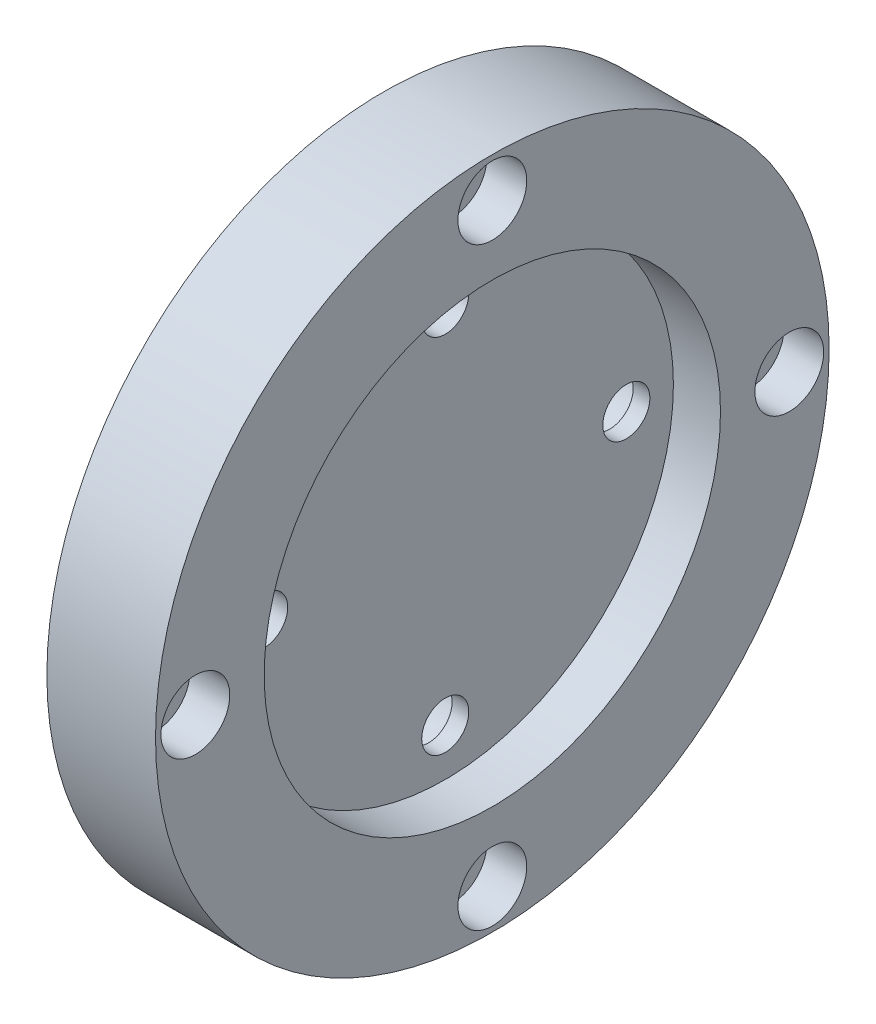
SolidWorks part; units mm, degrees
ref_plane "前视基准面" through (0, 0, 0) normal (0, 0, 1) x (1, 0, 0)
ref_plane "上视基准面" through (0, 0, 0) normal (0, 1, 0) x (1, 0, 0)
ref_plane "右视基准面" through (0, 0, 0) normal (1, 0, 0) x (0, 0, -1)
sketch "草图1" plane through (0, 0, 0) normal (1, 0, 0) x (0, 0, -1)
  circle A0 centre (0, 0) radius 46.5
  dimension "D1" = 93
extrude "凸台-拉伸1" add sketch "草图1" along normal blind 15
sketch "草图2" plane through (15, 0, 0) normal (1, 0, 0) x (0, 0, -1)
  circle A0 centre (0, 0) radius 31.5
  dimension "D1" = 63
extrude "切除-拉伸1" cut sketch "草图2" against normal blind 6.5
sketch "草图3" plane through (8.5, 0, 0) normal (1, 0, 0) x (0, 0, -1)
  circle A0 centre (0, 0) radius 25 construction
  circle A1 centre (0, 25) radius 3.25
  dimension "D1" = 50
  dimension "D2" = 6.5
extrude "切除-拉伸2" cut sketch "草图3" against normal through all
pattern_circular "阵列(圆周)1" count 4 over 360 about axis through (0, 0, 0) along (1, 0, 0) of "切除-拉伸2"
sketch "草图4" plane through (0, 0, 0) normal (-1, 0, 0) x (0, 0, 1)
  circle A0 centre (0, 25) radius 5.5
  circle A1 centre (-25, 0) radius 5.5
  circle A2 centre (0, -25) radius 5.5
  circle A3 centre (25, 0) radius 5.5
  dimension "D1" = 11
extrude "切除-拉伸3" cut sketch "草图4" against normal blind 6.2
sketch "草图5" plane through (15, 0, 0) normal (1, 0, 0) x (0, 0, -1)
  circle A0 centre (41, 0) radius 2.75
  dimension "D1" = 5.5
  dimension "D2" = 41
extrude "切除-拉伸4" cut sketch "草图5" against normal through all
pattern_circular "阵列(圆周)2" count 4 over 360 about axis through (0, 0, 0) along (1, 0, 0) of "切除-拉伸4"
sketch "草图6" plane through (15, 0, 0) normal (1, 0, 0) x (0, 0, -1)
  circle A0 centre (0, -41) radius 4.75
  dimension "D1" = 9.5
extrude "切除-拉伸5" cut sketch "草图6" against normal blind 5.5
pattern_circular "阵列(圆周)3" count 4 over 360 about axis through (0, 0, 0) along (1, 0, 0) of "切除-拉伸5"
